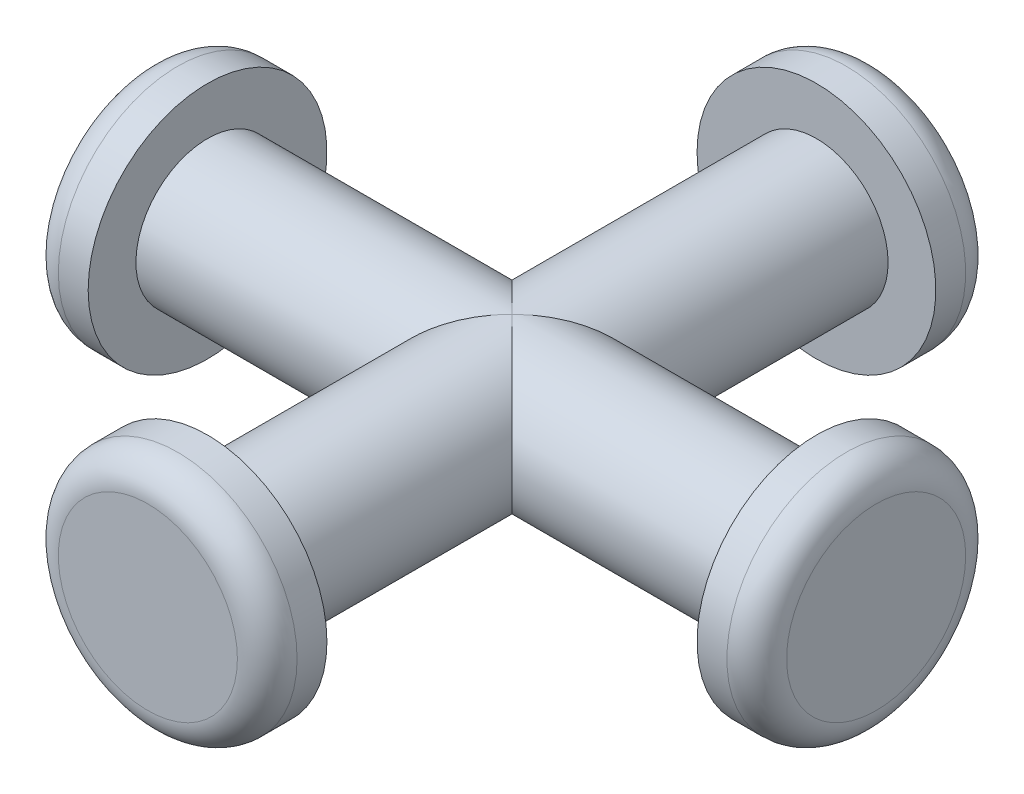
SolidWorks part; units mm, degrees
ref_plane "Plan de face" through (0, 0, 0) normal (0, 0, 1) x (1, 0, 0)
ref_plane "Plan de dessus" through (0, 0, 0) normal (0, 1, 0) x (1, 0, 0)
ref_plane "Plan de droite" through (0, 0, 0) normal (1, 0, 0) x (0, 0, -1)
sketch "Esquisse1" plane through (0, 0, 0) normal (0, 0, 1) x (1, 0, 0)
  circle A0 centre (0, 0) radius 2.4
  dimension "D1" = 4.8
extrude "Boss.-Extru.1" add sketch "Esquisse1" along normal mid plane 20.4 contours A0
sketch "Esquisse3" plane through (0, 0, 0) normal (1, 0, 0) x (0, 0, -1)
  circle A0 centre (0, 0) radius 2.4
  dimension "D1" = 4.8
extrude "Boss.-Extru.2" add sketch "Esquisse3" along normal mid plane 20.4
sketch "Esquisse4" plane through (10.2, 0, 0) normal (1, 0, 0) x (0, 0, -1)
  circle A0 centre (0, 0) radius 4
  dimension "D1" = 8
extrude "Boss.-Extru.3" add sketch "Esquisse4" along normal blind 2 contours A0
sketch "Esquisse5" plane through (-10.2, 0, 0) normal (-1, 0, 0) x (0, 0, 1)
  circle A0 centre (0, 0) radius 4
  dimension "D1" = 8
extrude "Boss.-Extru.4" add sketch "Esquisse5" along normal blind 2
sketch "Esquisse6" plane through (0, 0, 10.2) normal (0, 0, 1) x (1, 0, 0)
  circle A0 centre (0, 0) radius 4
  dimension "D1" = 8
extrude "Boss.-Extru.5" add sketch "Esquisse6" along normal blind 2
sketch "Esquisse7" plane through (0, 0, -10.2) normal (0, 0, -1) x (-1, 0, 0)
  circle A0 centre (0, 0) radius 4
  dimension "D1" = 8
extrude "Boss.-Extru.6" add sketch "Esquisse7" along normal blind 2 contours A0
fillet "Congé1" radius 1 4 edges at (-12.2, 0, 4) (-4, 0, -12.2) (12.2, 0, -4) (4, 0, 12.2)
